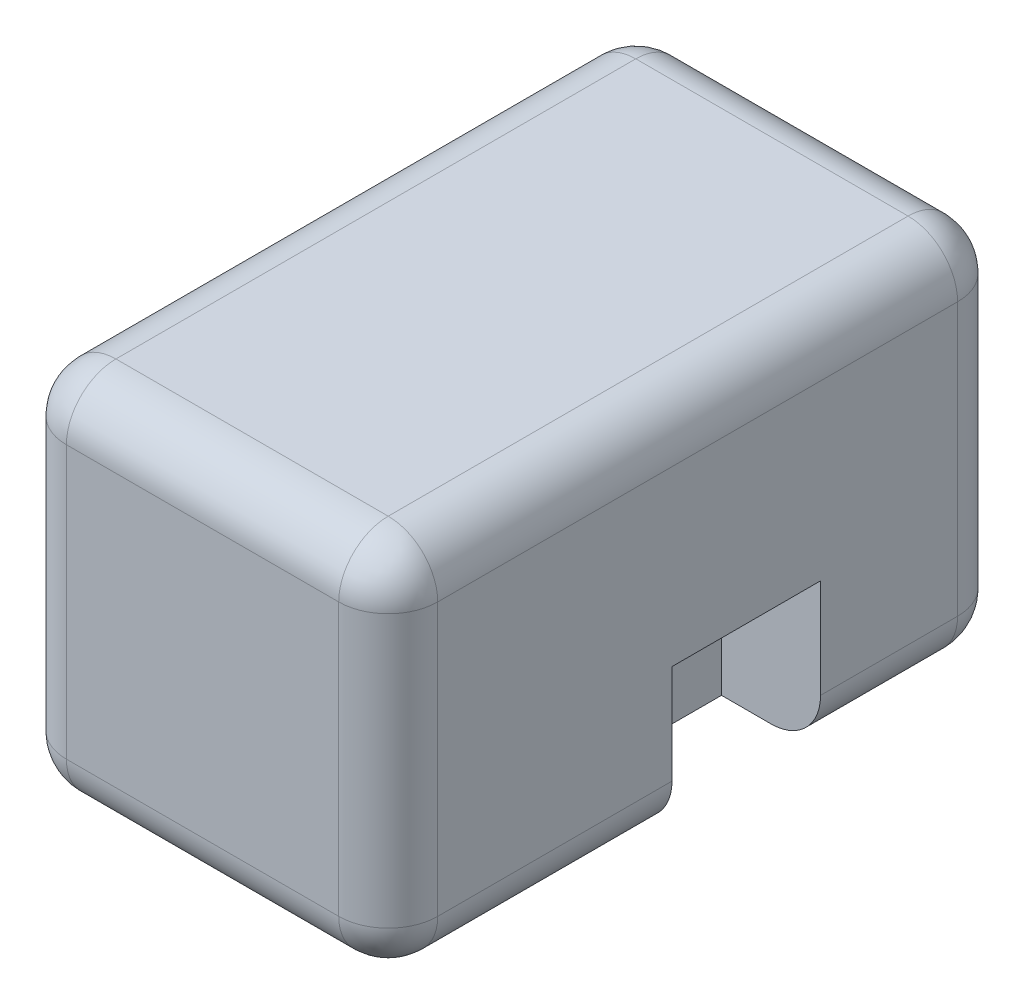
SolidWorks part; units mm, degrees
ref_plane "Plan de face" through (0, 0, 0) normal (0, 0, 1) x (1, 0, 0)
ref_plane "Plan de dessus" through (0, 0, 0) normal (0, 1, 0) x (1, 0, 0)
ref_plane "Plan de droite" through (0, 0, 0) normal (1, 0, 0) x (0, 0, -1)
sketch "Esquisse1" plane through (0, 0, 0) normal (0, 0, 1) x (1, 0, 0)
  line L1 (0, 0) -> (150, 0)
  line L2 (0, 0) -> (0, 150)
  line L3 (0, 150) -> (150, 150)
  line L4 (150, 0) -> (150, 150)
  dimension "D1" = 150
  dimension "D2" = 150
extrude "Boss.-Extru.1" add sketch "Esquisse1" along normal blind 250
fillet "Congé1" radius 20 12 edges at (150, 75, 250) (150, 75, 0) (150, 150, 125) (75, 150, 250) (75, 150, 0) (75, 0, 250) (150, 0, 125) (75, 0, 0) (0, 150, 125) (0, 75, 250) (0, 0, 125) (0, 75, 0)
sketch "Esquisse2" plane through (150, 0, 0) normal (1, 0, 0) x (0, 0, -1)
  line L1 (-135.3648, -19.9307) -> (-75.3648, -19.9307)
  line L2 (-135.3648, -19.9307) -> (-135.3648, 60.0693)
  line L3 (-135.3648, 60.0693) -> (-75.3648, 60.0693)
  line L4 (-75.3648, -19.9307) -> (-75.3648, 60.0693)
  dimension "D1" = 80
  dimension "D2" = 60
  dimension "D3" = 80
extrude "Enlèv. mat.-Extru.1" cut sketch "Esquisse2" against normal blind 40 contours L2 L3 L4 L1
sketch "Esquisse4" plane through (0, 0, 0) normal (-1, 0, 0) x (0, 0, 1)
  line L0 (230, 0) -> (20, 0) construction
  line L1 (75.5179, 60) -> (135.5179, 60)
  line L2 (75.5179, 60) -> (75.5179, 0)
  line L3 (75.5179, 0) -> (135.5179, 0)
  line L4 (135.5179, 60) -> (135.5179, 0)
  dimension "D1" = 60
  dimension "D2" = 60
extrude "Enlèv. mat.-Extru.2" cut sketch "Esquisse4" against normal blind 40
